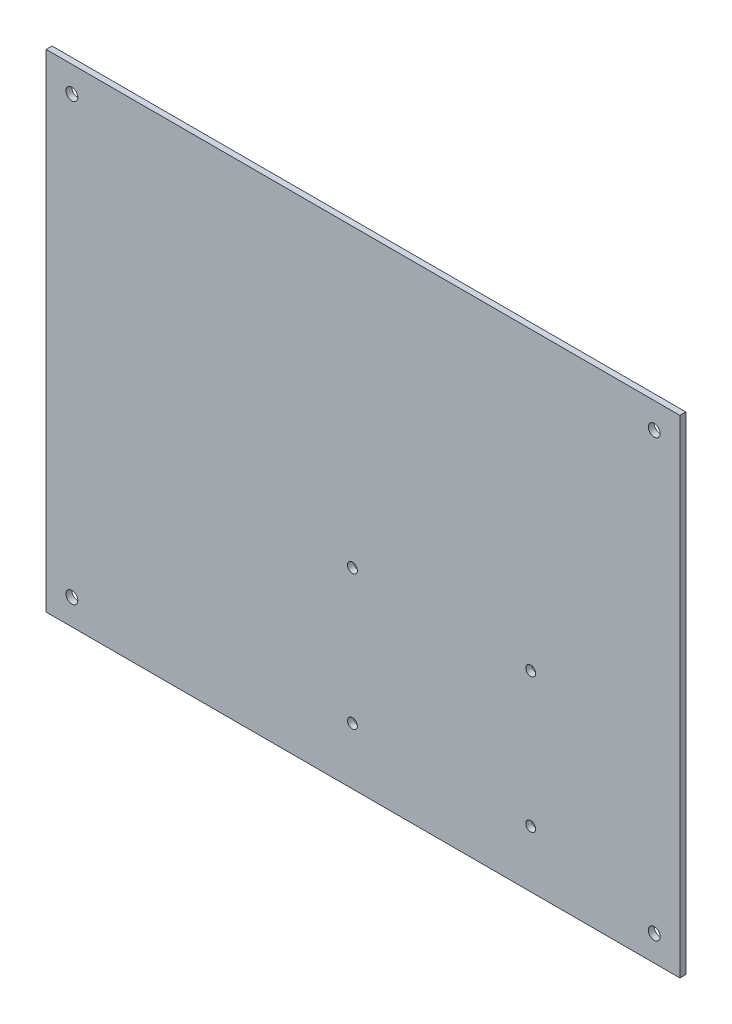
SolidWorks part; units mm, degrees
material "1060 合金"
ref_plane "前视基准面" through (0, 0, 0) normal (0, 0, 1) x (1, 0, 0)
ref_plane "上视基准面" through (0, 0, 0) normal (0, 1, 0) x (1, 0, 0)
ref_plane "右视基准面" through (0, 0, 0) normal (1, 0, 0) x (0, 0, -1)
sketch "草图1" plane through (0, 0, 0) normal (0, 0, 1) x (1, 0, 0)
  line L84 (352.6084, -1072.8029) -> (1952.6084, -1072.8029)
  line L85 (352.6084, -1072.8029) -> (352.6084, -2302.8029)
  line L86 (352.6084, -2302.8029) -> (1952.6084, -2302.8029)
  line L87 (1952.6084, -1072.8029) -> (1952.6084, -2302.8029)
  circle A108 centre (417.6084, -1137.8029) radius 15
  circle A109 centre (1887.6084, -1137.8029) radius 15
  circle A110 centre (1887.6084, -2237.8029) radius 15
  circle A111 centre (417.6084, -2237.8029) radius 15
  dimension "D25" = 1600
  dimension "D90" = 65
  dimension "D91" = 65
  dimension "D92" = 65
  dimension "D93" = 65
  dimension "D94" = 65
  dimension "D95" = 65
  dimension "D96" = 65
  dimension "D97" = 65
  dimension "D48" = 1230
extrude "凸台-拉伸1" add sketch "草图1" along normal blind 3
scale "缩放比例1" bodies to scale 101 104 102 103 108 scale about centroid uniform scaling no x scale factor 0.1 y scale factor 0.1 z scale factor 0.5
sketch "草图2" plane through (0, 0, 2.25) normal (0, 0, 1) x (1, 0, 0)
  line L0 (1072.6084, -1626.3029) -> (1072.6084, -1749.3029) construction
  line L7 (1072.6084, -1749.3029) -> (1232.6084, -1749.3029) construction
  circle A0 centre (1149.9339, -1700.9612) radius 1.25
  circle A1 centre (1194.9339, -1700.9612) radius 1.25
  circle A2 centre (1149.9339, -1734.9612) radius 1.25
  circle A3 centre (1194.9339, -1734.9612) radius 1.25
  dimension "D5" = 48.3417
  dimension "D1" = 2.5
  dimension "D2" = 77.3255
  dimension "D3" = 122.3255
  dimension "D4" = 14.3417
extrude "切除-拉伸4" cut sketch "草图2" against normal through all and the other way through all
